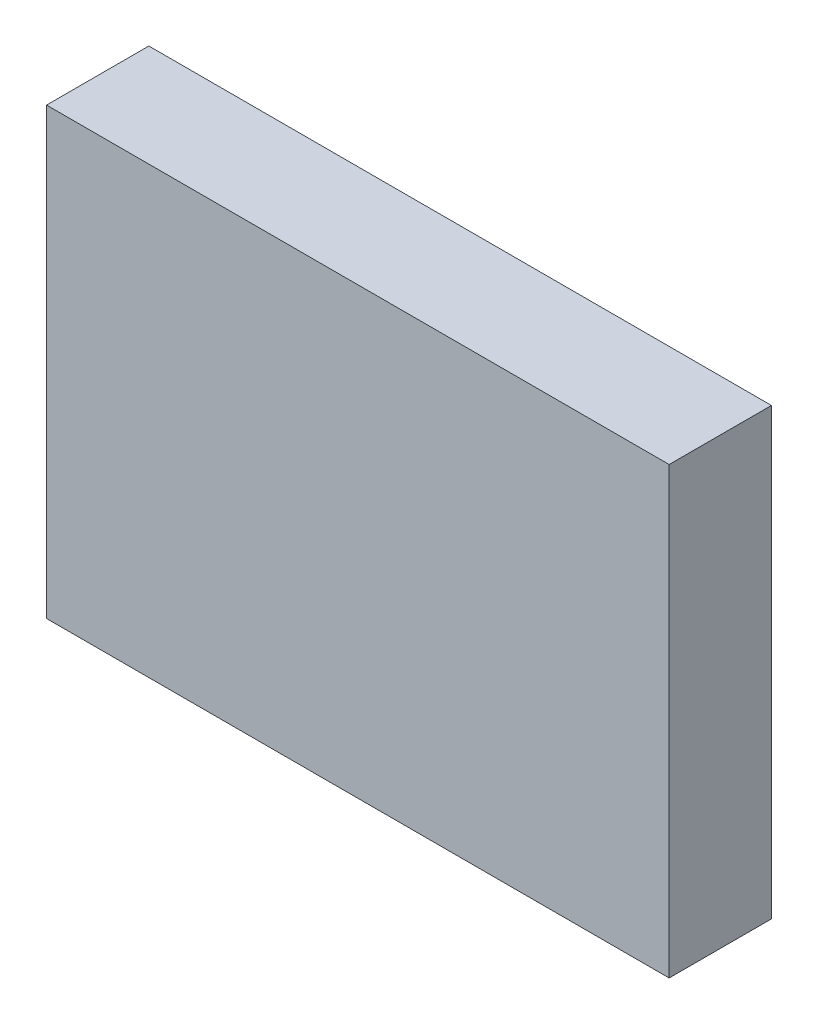
SolidWorks part; units mm, degrees
ref_plane "前视基准面" through (0, 0, 0) normal (0, 0, 1) x (1, 0, 0)
ref_plane "上视基准面" through (0, 0, 0) normal (0, 1, 0) x (1, 0, 0)
ref_plane "右视基准面" through (0, 0, 0) normal (1, 0, 0) x (0, 0, -1)
sketch "草图1" plane through (0, 0, 0) normal (0, 0, 1) x (1, 0, 0)
  line L0 (36.446, 19.6253) -> (50.446, 19.6253)
  line L1 (36.446, 29.6253) -> (50.446, 29.6253)
  line L2 (36.446, 29.6253) -> (36.446, 19.6253)
  line L3 (50.446, 29.6253) -> (50.446, 19.6253)
  dimension "D1" = 14
  dimension "D2" = 10
extrude "凸台-拉伸1" add sketch "草图1" along normal blind 2.3
